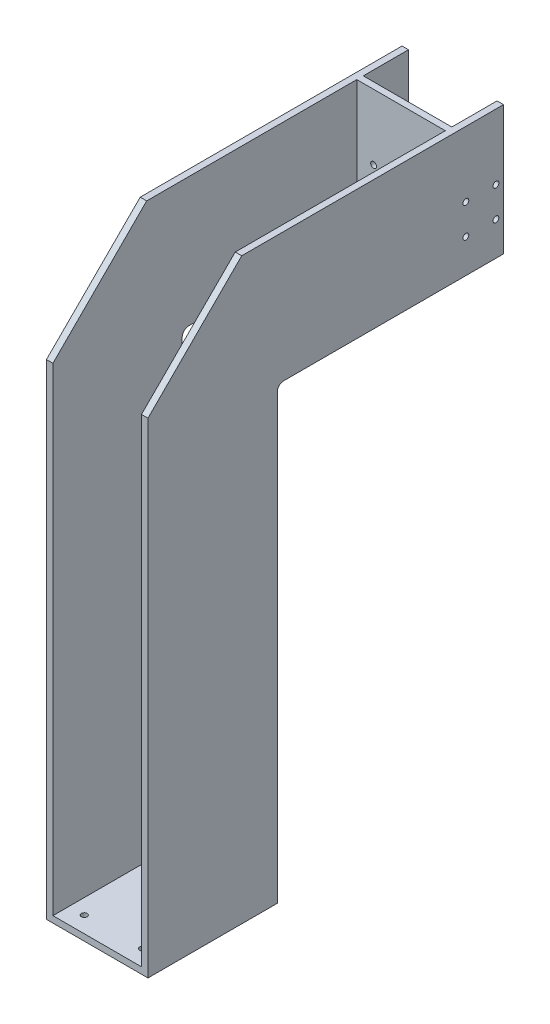
SolidWorks part; units mm, degrees
ref_plane "Front Plane" through (0, 0, 0) normal (0, 0, 1) x (1, 0, 0)
ref_plane "Top Plane" through (0, 0, 0) normal (0, 1, 0) x (1, 0, 0)
ref_plane "Right Plane" through (0, 0, 0) normal (1, 0, 0) x (0, 0, -1)
sketch "Sketch1" plane through (0, 0, 0) normal (1, 0, 0) x (0, 0, -1)
  line L0 (0, 0) -> (0, 750)
  line L1 (0, 750) -> (145, 895)
  line L2 (145, 895) -> (550, 895)
  line L3 (550, 895) -> (550, 695)
  line L6 (200, 0) -> (0, 0)
  line L11 (200, 0) -> (200, 695)
  line L12 (200, 695) -> (550, 695)
  dimension "D1" = 200
  dimension "D2" = 895
  dimension "D3" = 750
  dimension "D4" = 200
  dimension "D5" = 550
  dimension "D6" = 45
extrude "Boss-Extrude1" add sketch "Sketch1" along normal blind 10 and the other way blind 147
sketch "Sketch3" plane through (0, 895, 0) normal (0, 1, 0) x (1, 0, 0)
  line L0 (-147, 550) -> (10, 550) construction
  line L1 (-137, 550) -> (0, 550)
  line L2 (-137, 550) -> (-137, 0)
  line L3 (-137, 0) -> (0, 0)
  line L4 (0, 550) -> (0, 0)
  line L5 (-147, 0) -> (10, 0) construction
  point P8 (-68.5, 550)
  point P9 (-68.5, 550)
  dimension "D1" = 137
extrude "Cut-Extrude1" cut sketch "Sketch3" against normal offset from surface (885 mm away) 10 up to face at (-68.5, 0, -100)
ref_plane "Plane1" through (0, 0, -480) normal (0, 0, -1) x (-1, 0, 0)
sketch "Sketch4" plane through (0, 0, -480) normal (0, 0, -1) x (-1, 0, 0)
  line L1 (0, 895) -> (137, 895)
  line L2 (0, 895) -> (0, 695)
  line L3 (0, 695) -> (137, 695)
  line L4 (137, 895) -> (137, 695)
extrude "Boss-Extrude2" add sketch "Sketch4" against normal blind 10 contours L2 L1 L4 L3
sketch "Sketch5" plane through (10, 0, 0) normal (1, 0, 0) x (0, 0, -1)
  line L0 (200, 695) -> (550, 695) construction
  line L2 (515, 895) -> (515, 695) construction
  line L5 (550, 895) -> (145, 895) construction
  line L6 (550, 695) -> (550, 895) construction
  line L7 (491.75, 793.7) -> (538.25, 793.7) construction
  circle A0 centre (538.25, 747.2) radius 4.5
  circle A1 centre (538.25, 793.7) radius 4.5
  circle A2 centre (491.75, 747.2) radius 4.5
  circle A3 centre (491.75, 793.7) radius 4.5
  point P17 (515, 793.7)
  dimension "D4" = 9
  dimension "D1" = 52.2
  dimension "D2" = 46.5
  dimension "D3" = 46.5
  dimension "D5" = 35
extrude "Cut-Extrude2" cut sketch "Sketch5" against normal through all
sketch "Sketch6" plane through (0, 0, -470) normal (0, 0, 1) x (1, 0, 0)
  line L0 (0, 695) -> (-137, 695) construction
  line L1 (-111, 747.2) -> (-26, 747.2) construction
  line L2 (0, 895) -> (-137, 895) construction
  line L3 (0, 895) -> (0, 695) construction
  circle A0 centre (-111, 747.2) radius 4.5
  circle A1 centre (-26, 747.2) radius 4.5
  circle A2 centre (-111, 793.7) radius 4.5
  circle A3 centre (-26, 793.7) radius 4.5
  circle A4 centre (-63, 788.5) radius 8
  point P10 (-68.5, 895)
  point P11 (-68.5, 747.2)
  dimension "D3" = 9
  dimension "D5" = 16
  dimension "D1" = 52.2
  dimension "D2" = 85
  dimension "D4" = 46.5
  dimension "D6" = 93.5
  dimension "D7" = 63
extrude "Cut-Extrude3" cut sketch "Sketch6" against normal up to next
sketch "Sketch7" plane through (0, 10, 0) normal (0, 1, 0) x (1, 0, 0)
  line L1 (-113.5, 25) -> (-23.5, 25) construction
  line L2 (-23.5, 25) -> (-23.5, 175) construction
  line L3 (0, 0) -> (0, 200) construction
  line L4 (-137, 0) -> (0, 0) construction
  circle A0 centre (-113.5, 175) radius 4.5
  circle A1 centre (-23.5, 175) radius 4.5
  circle A2 centre (-23.5, 25) radius 4.5
  circle A3 centre (-113.5, 25) radius 4.5
  circle A4 centre (-113.5, 155) radius 5
  circle A5 centre (-23.5, 45) radius 5
  point P14 (0, 100)
  point P15 (-23.5, 100)
  point P18 (-68.5, 0)
  point P19 (-68.5, 25)
  dimension "D1" = 10
  dimension "D2" = 9
  dimension "D3" = 90
  dimension "D4" = 150
  dimension "D5" = 20
  dimension "D6" = 20
extrude "Cut-Extrude4" cut sketch "Sketch7" against normal up to next
fillet "Fillet1" radius 10 2 edges at (-142, 695, -200) (5, 695, -200)
